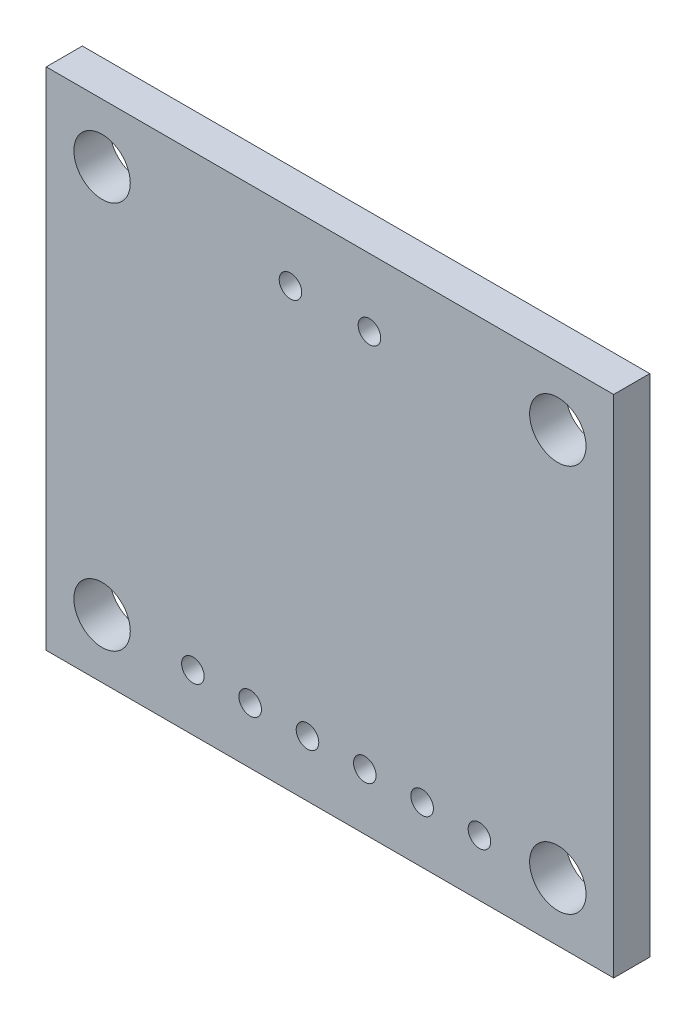
SolidWorks part; units mm, degrees
ref_plane "Front Plane" through (0, 0, 0) normal (0, 0, 1) x (1, 0, 0)
ref_plane "Top Plane" through (0, 0, 0) normal (0, 1, 0) x (1, 0, 0)
ref_plane "Right Plane" through (0, 0, 0) normal (1, 0, 0) x (0, 0, -1)
sketch "Sketch1" plane through (0, 0, 0) normal (0, 0, 1) x (1, 0, 0)
  line L0 (-10.1, 8.6) -> (10.1, -8.6) construction
  line L1 (-12.575, -11.2) -> (12.575, -11.2)
  line L2 (-12.575, -11.2) -> (-12.575, 11.2)
  line L3 (-12.575, 11.2) -> (12.575, 11.2)
  line L4 (12.575, -11.2) -> (12.575, 11.2)
  line L5 (-12.575, -11.2) -> (12.575, 11.2) construction
  line L6 (-12.575, 11.2) -> (12.575, -11.2) construction
  line L7 (-1.75, 8.2) -> (1.75, 8.2) construction
  circle A0 centre (-10.1, 8.6) radius 1.25
  circle A1 centre (10.1, 8.6) radius 1.25
  circle A2 centre (-10.1, -8.6) radius 1.25
  circle A3 centre (10.1, -8.6) radius 1.25
  circle A4 centre (-1.75, 8.2) radius 0.5
  circle A5 centre (1.75, 8.2) radius 0.5
  circle A6 centre (-6.075, -8.7) radius 0.5
  circle A7 centre (-3.535, -8.7) radius 0.5
  circle A8 centre (-0.995, -8.7) radius 0.5
  circle A9 centre (1.545, -8.7) radius 0.5
  circle A10 centre (4.085, -8.7) radius 0.5
  circle A11 centre (6.625, -8.7) radius 0.5
  point P0 (0, 0)
  point P14 (0, 0)
  point P17 (0, 8.2)
  point P32 (0, 0)
  dimension "D5" = 2.5
  dimension "D6" = 1
  dimension "D9" = 1
  dimension "D1" = 22.4
  dimension "D2" = 25.15
  dimension "D3" = 20.2
  dimension "D4" = 17.2
  dimension "D7" = 3.5
  dimension "D8" = 3
  dimension "D10" = 6.5
  dimension "D11" = 2.5
  dimension "D12" = 2.54
  dimension "D13" = 2.54
  dimension "D14" = 2.54
  dimension "D15" = 2.54
  dimension "D16" = 2.54
extrude "Boss-Extrude1" add sketch "Sketch1" along normal blind 1.6
